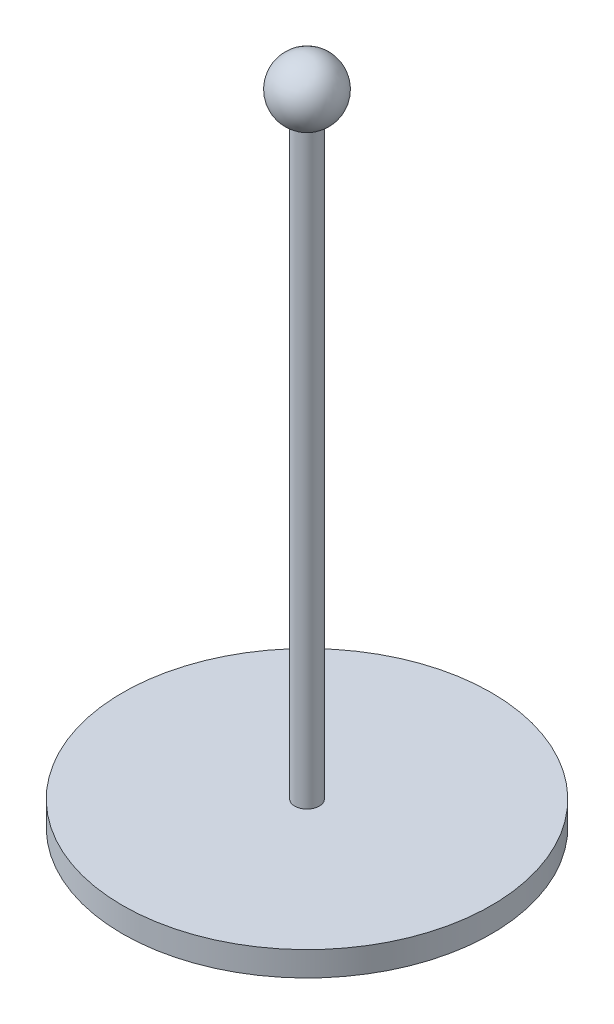
SolidWorks part; units mm, degrees
material "Aço carbono simples"
ref_plane "Plano frontal" through (0, 0, 0) normal (0, 0, 1) x (1, 0, 0)
ref_plane "Plano superior" through (0, 0, 0) normal (0, 1, 0) x (1, 0, 0)
ref_plane "Plano direito" through (0, 0, 0) normal (1, 0, 0) x (0, 0, -1)
sketch "Esboço1" plane through (0, 0, 0) normal (0, 1, 0) x (1, 0, 0)
  circle A0 centre (0, 0) radius 75
  dimension "D1" = 150
extrude "Ressalto-extrusão1" add sketch "Esboço1" along normal blind 10
sketch "Esboço2" plane through (0, 10, 0) normal (0, 1, 0) x (1, 0, 0)
  circle A0 centre (0, 0) radius 5
extrude "Ressalto-extrusão2" add sketch "Esboço2" along normal blind 250
sketch "Esboço4" plane through (0, 0, 0) normal (1, 0, 0) x (0, 0, -1)
  line L0 (5, 260) -> (-5, 260) construction
  line L1 (0, 272.5) -> (0, 247.5)
  arc A0 (0, 247.5) -> (0, 272.5) centre (0, 260) ccw
  dimension "D1" = 25
revolve "Revolução1" add sketch "Esboço4" angle 360 about L1
